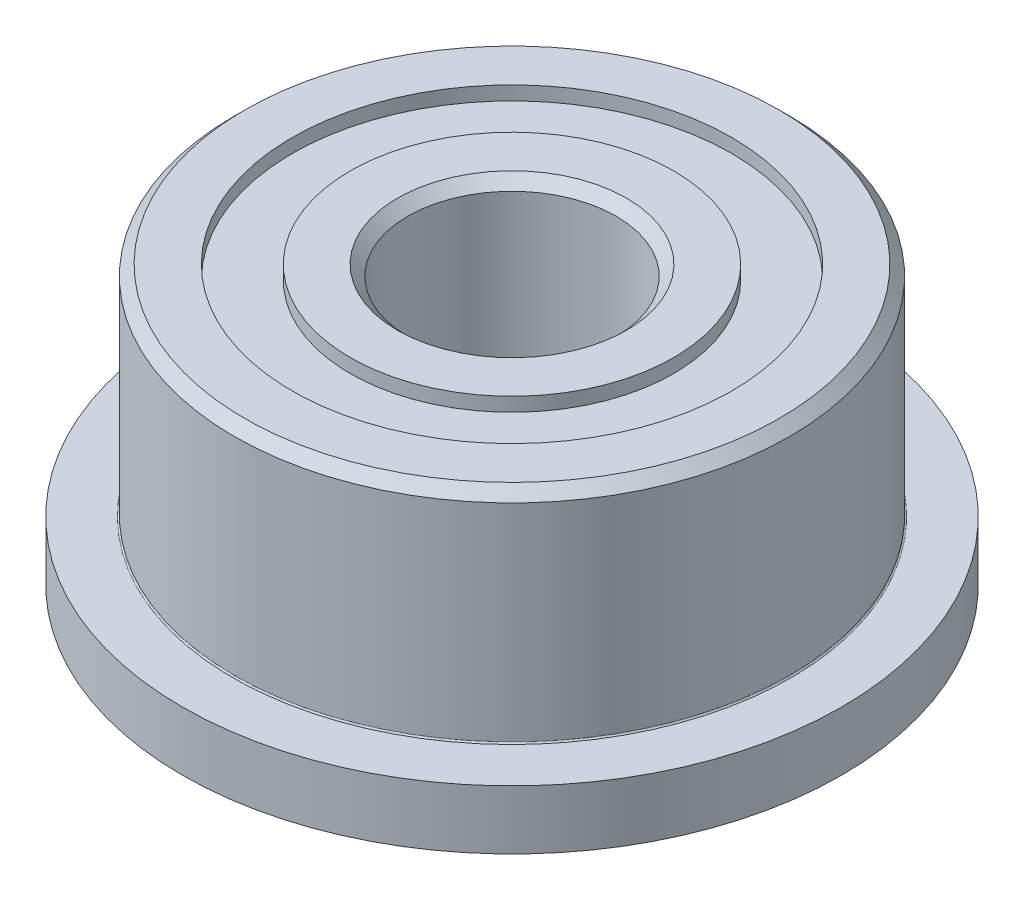
SolidWorks part; units mm, degrees
material "1023 Carbon Steel Sheet (SS)"
ref_plane "Front Plane" through (0, 0, 0) normal (0, 0, 1) x (1, 0, 0)
ref_plane "Top Plane" through (0, 0, 0) normal (0, 1, 0) x (1, 0, 0)
ref_plane "Right Plane" through (0, 0, 0) normal (1, 0, 0) x (0, 0, -1)
ref_plane "Plane1" through (0, 0, 50.5748) normal (0, 0, 1) x (1, 0, 0)
sketch "Sketch1" plane through (0, 0, 50.5748) normal (0, 0, 1) x (1, 0, 0)
  line L0 (-85.2681, -0.65) -> (-84.4331, -0.65)
  line L1 (-84.4331, -0.65) -> (-84.4331, -0.85)
  line L2 (-84.4331, -0.85) -> (-82.8481, -0.85)
  line L3 (-82.8481, -0.85) -> (-82.8481, 0)
  line L4 (-82.8481, 0) -> (-83.5781, 0)
  line L5 (-83.5981, 0.02) -> (-83.5981, 3)
  line L6 (-83.5981, 3) -> (-83.7481, 3.15)
  line L7 (-83.7481, 3.15) -> (-84.4331, 3.15)
  line L8 (-84.4331, 3.15) -> (-84.4331, 2.95)
  line L9 (-84.4331, 2.95) -> (-85.2681, 2.95)
  line L10 (-85.2681, 2.95) -> (-85.2681, 3.15)
  line L11 (-85.2681, 3.15) -> (-85.9481, 3.15)
  line L12 (-85.9481, 3.15) -> (-86.0981, 3)
  line L13 (-86.0981, 3) -> (-86.0981, -0.7)
  line L14 (-86.0981, -0.7) -> (-85.9481, -0.85)
  line L15 (-85.9481, -0.85) -> (-85.2681, -0.85)
  line L16 (-85.2681, -0.85) -> (-85.2681, -0.65)
  line L17 (-87.5981, 3.15) -> (-87.5981, -0.85) construction
  spline S0 degree 3 poles (-83.5781, 0) (-83.5781, -0.0246) (-83.6228, 0.02) (-83.5981, 0.02) knots 0 0 0 0 1 1 1 1
revolve "Revolve1" add sketch "Sketch1" angle 360 about L17
